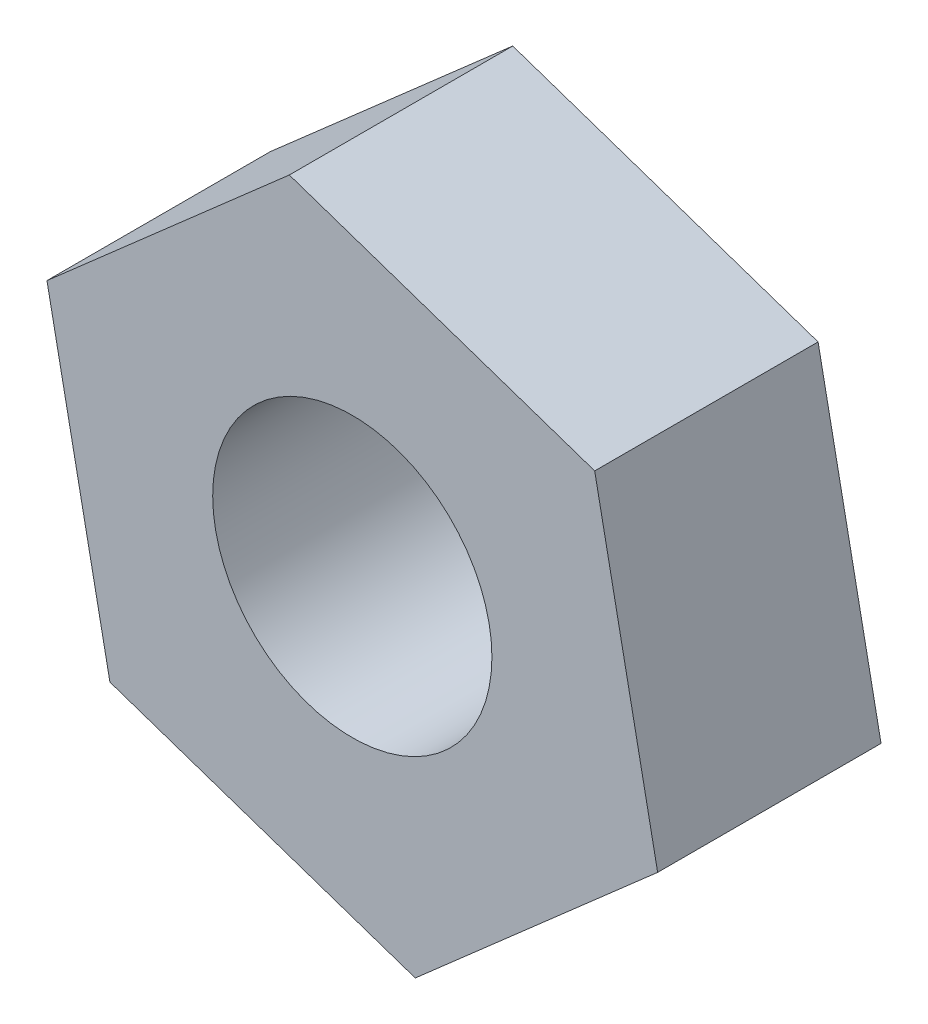
SolidWorks part; units mm, degrees
ref_plane "前视基准面" through (0, 0, 0) normal (0, 0, 1) x (1, 0, 0)
ref_plane "上视基准面" through (0, 0, 0) normal (0, 1, 0) x (1, 0, 0)
ref_plane "右视基准面" through (0, 0, 0) normal (1, 0, 0) x (0, 0, -1)
sketch "草图1" plane through (0, 0, 0) normal (0, 0, 1) x (1, 0, 0)
  line L1 (2.7337, -0.9274) -> (2.17, 1.9038)
  line L2 (2.17, 1.9038) -> (-0.5637, 2.8312)
  line L3 (-0.5637, 2.8312) -> (-2.7337, 0.9274)
  line L4 (-2.7337, 0.9274) -> (-2.17, -1.9038)
  line L5 (-2.17, -1.9038) -> (0.5637, -2.8312)
  line L6 (0.5637, -2.8312) -> (2.7337, -0.9274)
  circle A0 centre (0, 0) radius 2.5 construction
  circle A1 centre (0, 0) radius 1.25
  dimension "D2" = 2.5
  dimension "D1" = 5
extrude "凸台-拉伸1" add sketch "草图1" along normal blind 2
